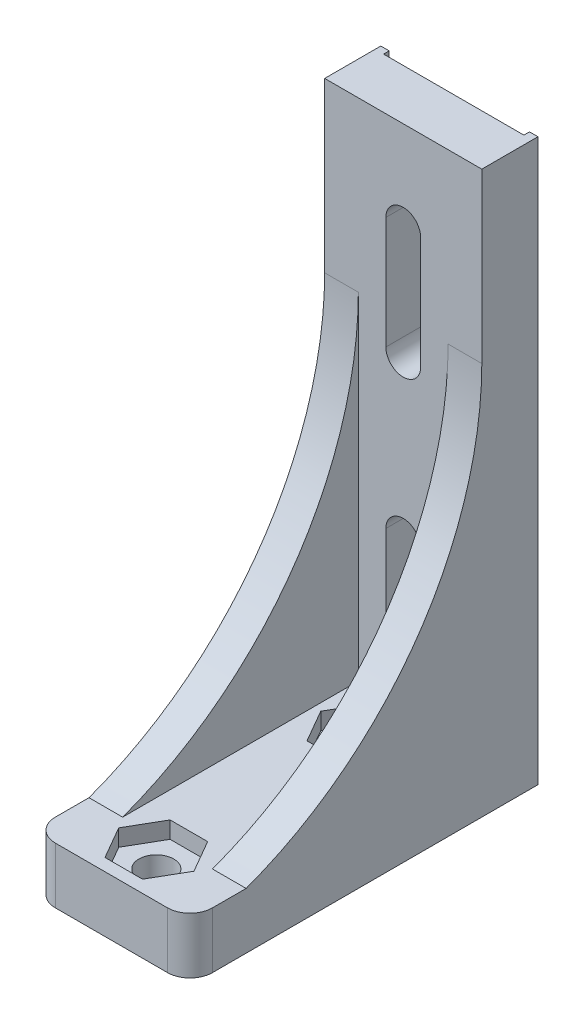
SolidWorks part; units mm, degrees
ref_plane "Alzado" through (0, 0, 0) normal (0, 0, 1) x (1, 0, 0)
ref_plane "Planta" through (0, 0, 0) normal (0, 1, 0) x (1, 0, 0)
ref_plane "Vista lateral" through (0, 0, 0) normal (1, 0, 0) x (0, 0, -1)
sketch "Croquis2" plane through (0, 0, 0) normal (0, 1, 0) x (1, 0, 0)
  line L0 (7, 31) -> (7, 0) construction
  line L1 (0, 0) -> (14, 0)
  line L2 (0, 0) -> (0, 31)
  line L3 (0, 31) -> (14, 31)
  line L4 (14, 0) -> (14, 31)
  circle A0 centre (7, 22) radius 1.55
  circle A1 centre (7, 4) radius 1.55
  dimension "D3" = 3.1
  dimension "D4" = 18
  dimension "D5" = 4
  dimension "D1" = 14
  dimension "D2" = 31
extrude "Saliente-Extruir1" add sketch "Croquis2" along normal blind 50
sketch "Croquis3" plane through (0, 0, 0) normal (-1, 0, 0) x (0, 0, 1)
  line L0 (-31, 50) -> (-31, 0) construction
  line L1 (0, 50) -> (-26, 50)
  line L2 (0, 50) -> (0, 5)
  line L3 (0, 5) -> (-26, 5)
  line L4 (-26, 50) -> (-26, 5)
  line L5 (-31, 0) -> (0, 0) construction
  dimension "D1" = 5
  dimension "D2" = 5
extrude "Cortar-Extruir1" cut sketch "Croquis3" against normal up to surface (14 mm away) up to face at (14, 25, -15.5)
sketch "Croquis4" plane through (0, 0, -31) normal (0, 0, -1) x (-1, 0, 0)
  line L0 (-7, 0) -> (-7, 50) construction
  line L1 (-14, 0) -> (0, 0) construction
  line L2 (-14, 50) -> (0, 50) construction
  line L3 (-14, 50) -> (-14, 0) construction
  line L5 (-7, 8) -> (-7, 18) construction
  line L6 (-8.55, 8) -> (-8.55, 18)
  line L7 (-5.45, 8) -> (-5.45, 18)
  line L8 (-7, 32) -> (-7, 42) construction
  line L9 (-8.55, 32) -> (-8.55, 42)
  line L10 (-5.45, 32) -> (-5.45, 42)
  arc A0 (-8.55, 8) -> (-5.45, 8) centre (-7, 8) ccw
  arc A1 (-5.45, 18) -> (-8.55, 18) centre (-7, 18) ccw
  arc A2 (-8.55, 32) -> (-5.45, 32) centre (-7, 32) ccw
  arc A3 (-5.45, 42) -> (-8.55, 42) centre (-7, 42) ccw
  point P8 (-7, 13)
  point P17 (-7, 37)
  dimension "D1" = 7
  dimension "D2" = 3.1
  dimension "D3" = 10
  dimension "D4" = 3.1
  dimension "D5" = 10
  dimension "D6" = 8
  dimension "D7" = 14
extrude "Cortar-Extruir2" cut sketch "Croquis4" against normal up to surface (5 mm away) up to face at (7, 27.5, -26)
sketch "Croquis5" plane through (0, 5, 0) normal (0, 1, 0) x (1, 0, 0)
  line L1 (10.3486, 4) -> (8.6743, 6.9)
  line L2 (8.6743, 6.9) -> (5.3257, 6.9)
  line L3 (5.3257, 6.9) -> (3.6514, 4)
  line L4 (3.6514, 4) -> (5.3257, 1.1)
  line L5 (5.3257, 1.1) -> (8.6743, 1.1)
  line L6 (8.6743, 1.1) -> (10.3486, 4)
  line L7 (8.6743, 19.1) -> (10.3486, 22)
  line L8 (10.3486, 22) -> (8.6743, 24.9)
  line L9 (8.6743, 24.9) -> (5.3257, 24.9)
  line L10 (5.3257, 24.9) -> (3.6514, 22)
  line L11 (3.6514, 22) -> (5.3257, 19.1)
  line L12 (5.3257, 19.1) -> (8.6743, 19.1)
  circle A0 centre (7, 4) radius 2.9 construction
  circle A1 centre (7, 22) radius 2.9 construction
  dimension "D1" = 5.8
  dimension "D2" = 5.8
extrude "Cortar-Extruir3" cut sketch "Croquis5" against normal blind 1.5
sketch "Croquis6" plane through (0, 0, 0) normal (-1, 0, 0) x (0, 0, 1)
  line L3 (-26, 50) -> (-26, 5) construction
  line L9 (-26, 5) -> (0, 5) construction
  line L10 (-31, 50) -> (-26, 50) construction
  line L11 (0, 5) -> (0, 0) construction
  line L12 (-26, 5) -> (-26, 35)
  line L13 (-26, 5) -> (-5, 5)
  arc A1 (-26, 35) -> (-5, 5) centre (5.9975, 35.0482) ccw
  dimension "D1" = 15
  dimension "D2" = 5
extrude "Saliente-Extruir3" add sketch "Croquis6" against normal up to surface (14 mm away) up to face at (14, 18.3333, -19)
sketch "Croquis7" plane through (0, 50, 0) normal (0, 1, 0) x (1, 0, 0)
  line L0 (14, 0) -> (0, 0) construction
  line L2 (0, 26) -> (0, 0)
  line L3 (0, 0) -> (3, 0)
  line L4 (3, 26) -> (3, 0)
  line L7 (14, 26) -> (14, 0)
  line L8 (14, 0) -> (11, 0)
  line L9 (11, 26) -> (11, 0)
  line L10 (3, 26) -> (11, 26)
  line L11 (0, 26) -> (0, 31)
  line L12 (0, 31) -> (14, 31)
  line L13 (14, 26) -> (14, 31)
  dimension "D1" = 3
  dimension "D2" = 3
  dimension "D3" = 5
extrude "Cortar-Extruir5" cut sketch "Croquis7" against normal up to surface (45 mm away) flip side to cut up to face at (7, 5, -3.02)
fillet "Redondeo1" radius 2 2 edges at (14, 2.5, 0) (0, 2.5, 0)
sketch "Croquis8" plane through (0, 50, 0) normal (0, 1, 0) x (1, 0, 0)
  line L0 (14, 31) -> (0, 31) construction
  line L1 (0.75, 31) -> (13.25, 31)
  line L2 (0.75, 31) -> (0.75, 30.5)
  line L3 (0.75, 30.5) -> (13.25, 30.5)
  line L4 (13.25, 31) -> (13.25, 30.5)
  line L5 (0, 31) -> (0, 26) construction
  dimension "D1" = 12.5
  dimension "D2" = 0.75
  dimension "D3" = 0.5
extrude "Cortar-Extruir6" cut sketch "Croquis8" against normal up to surface (50 mm away) up to face at (7, 0, -20.45)
